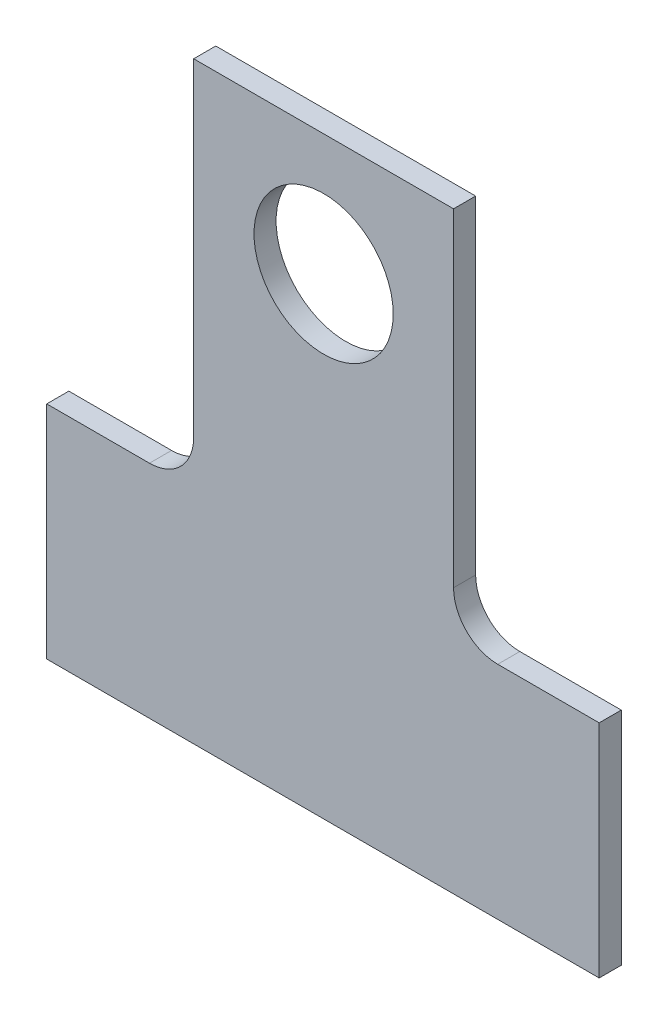
SolidWorks part; units mm, degrees
material "Nikiel"
ref_plane "Płaszczyzna przednia" through (0, 0, 0) normal (0, 0, 1) x (1, 0, 0)
ref_plane "Płaszczyzna górna" through (0, 0, 0) normal (0, 1, 0) x (1, 0, 0)
ref_plane "Płaszczyzna prawa" through (0, 0, 0) normal (1, 0, 0) x (0, 0, -1)
sketch "Szkic1" plane through (0, 0, 0) normal (0, 0, 1) x (1, 0, 0)
  line L6 (-12.5, -6) -> (-12.5, -16)
  line L10 (-12.5, -16) -> (12.5, -16)
  line L11 (12.5, -16) -> (12.5, -6)
  line L12 (7.91, -6) -> (12.5, -6)
  line L13 (-7.85, -6) -> (-12.5, -6)
  line L17 (-5.85, 5.45) -> (-5.85, 6.85)
  line L19 (5.91, 6.85) -> (5.91, 5.45)
  line L20 (-5.85, -4) -> (-5.85, 5.45)
  line L22 (5.91, 5.45) -> (5.91, -4)
  line L23 (-5.85, 6.85) -> (-5.85, 10.85)
  line L24 (-5.85, 10.85) -> (5.91, 10.85)
  line L25 (5.91, 10.85) -> (5.91, 6.85)
  arc A0 (-5.85, -4) -> (-7.85, -6) centre (-7.85, -4) cw
  arc A5 (5.91, -4) -> (7.91, -6) centre (7.91, -4) ccw
  point P0 (0, 0)
  dimension "D1" = 2
  dimension "D2" = 25
  dimension "D3" = 10
extrude "Dodanie-wyciągnięcie1" add sketch "Szkic1" along normal blind 1
sketch "Szkic2" plane through (0, 0, 1) normal (0, 0, 1) x (1, 0, 0)
  circle A14 centre (0.03, 5.36) radius 3.15
extrude "Wytnij-wyciągnięcie1" cut sketch "Szkic2" against normal blind 1
